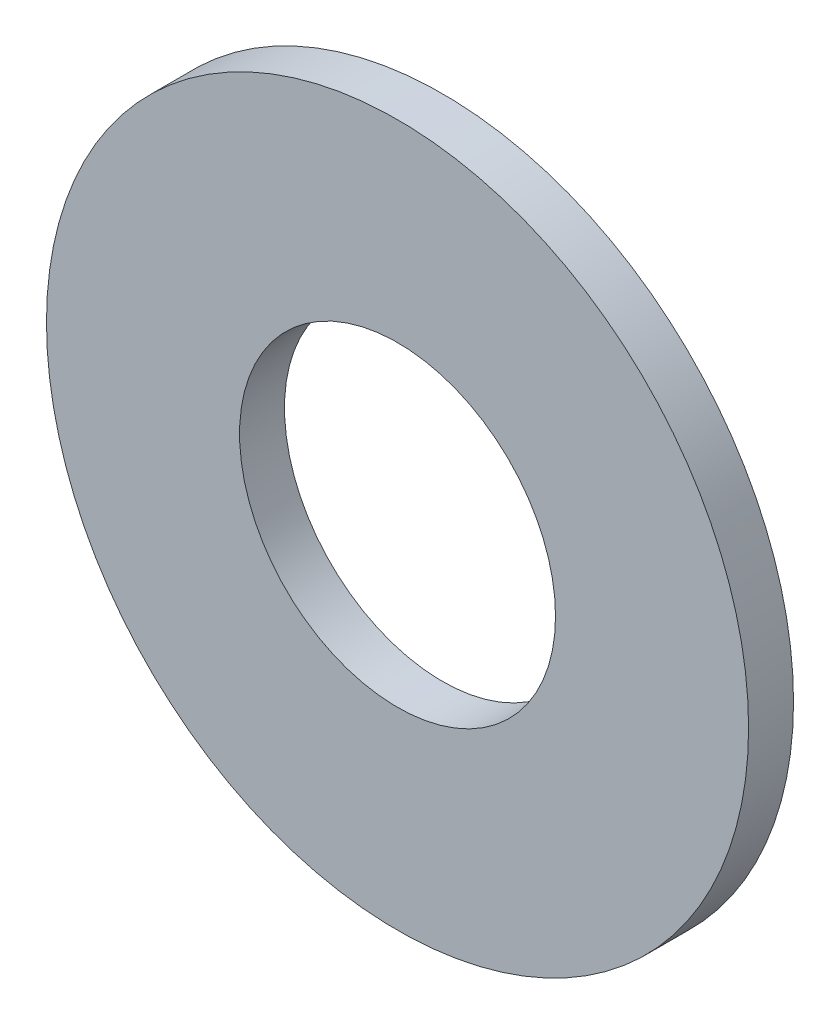
SolidWorks part; units mm, degrees
ref_plane "Front Plane" through (0, 0, 0) normal (0, 0, 1) x (1, 0, 0)
ref_plane "Top Plane" through (0, 0, 0) normal (0, 1, 0) x (1, 0, 0)
ref_plane "Right Plane" through (0, 0, 0) normal (1, 0, 0) x (0, 0, -1)
sketch "Sketch1" plane through (0, 0, 0) normal (0, 0, 1) x (1, 0, 0)
  circle A0 centre (0, 0) radius 3.5719
  circle A1 centre (0, 0) radius 7.9375
  dimension "ID" = 7.1437
  dimension "OD" = 15.875
extrude "Extrude1" add sketch "Sketch1" against normal blind 1.016
